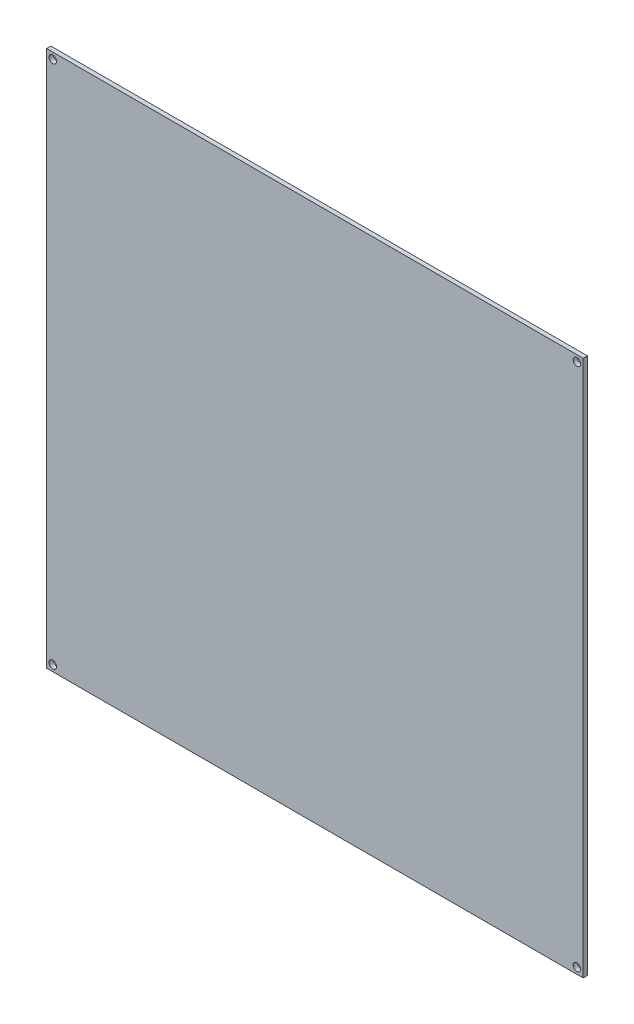
SolidWorks part; units mm, degrees
material "A-Fibra di vetro"
ref_plane "Piano frontale" through (0, 0, 0) normal (0, 0, 1) x (1, 0, 0)
ref_plane "Piano superiore" through (0, 0, 0) normal (0, 1, 0) x (1, 0, 0)
ref_plane "Piano destro" through (0, 0, 0) normal (1, 0, 0) x (0, 0, -1)
sketch "Schizzo1" plane through (0, 0, 0) normal (0, 0, 1) x (1, 0, 0)
  line L0 (214, 214) -> (0, 0) construction
  line L1 (0, 0) -> (214, 0)
  line L2 (0, 0) -> (0, 214)
  line L3 (0, 214) -> (214, 214)
  line L4 (214, 0) -> (214, 214)
  line L5 (214, 0) -> (0, 214) construction
  dimension "D1" = 214
  dimension "D2" = 214
sketch "Schizzo2" plane through (0, 0, 0) normal (0, 0, 1) x (1, 0, 0)
  line L0 (107, 214) -> (107, 0) construction
  line L1 (0, 0) -> (214, 0)
  line L2 (0, 0) -> (0, 214)
  line L3 (0, 214) -> (214, 214)
  line L4 (214, 0) -> (214, 214)
  line L5 (214, 107) -> (0, 107) construction
  line L6 (214, 0) -> (0, 214) construction
  circle A0 centre (2.5, 211.5) radius 1.5
  circle A1 centre (211.5, 211.5) radius 1.5
  circle A2 centre (211.5, 2.5) radius 1.5
  circle A3 centre (2.5, 2.5) radius 1.5
  dimension "D1" = 3
  dimension "D2" = 104.5
extrude "Estrusione-Estrusione2" add sketch "Schizzo2" against normal blind 1.7
